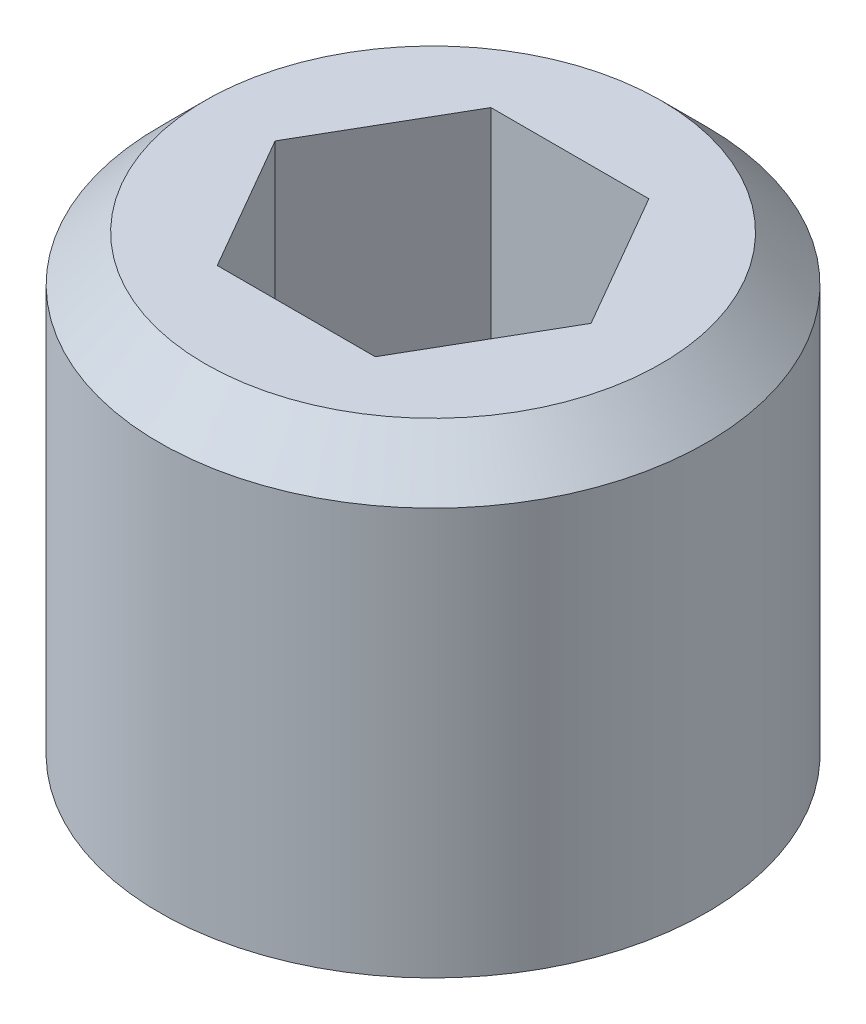
SolidWorks part; units mm, degrees
material "Alloy Steel"
ref_plane "Plane1" through (0, 0, 0) normal (0, 0, 1) x (1, 0, 0)
ref_plane "Plane2" through (0, 0, 0) normal (0, 1, 0) x (1, 0, 0)
ref_plane "Plane3" through (0, 0, 0) normal (1, 0, 0) x (0, 0, -1)
sketch "Sketch1" plane through (0, 0, 0) normal (0, 0, 1) x (1, 0, 0)
  line L0 (0, 0.3464) -> (0, 3)
  line L1 (0, 3) -> (1.25, 3)
  line L2 (0.6, 0) -> (0, 0.3464)
  line L3 (1.5, 2.75) -> (1.25, 3)
  line L4 (1.5, 2.75) -> (1.5, 0.5196)
  line L5 (1.5, 0.5196) -> (0.6, 0)
  line L6 (0, 3) -> (0, 5.6536) construction
  dimension "D6" = 3
  dimension "D1" = 0.25
  dimension "D2" = 0.25
  dimension "D3" = 3
  dimension "D4" = 1.2
  dimension "D5" = 60
  dimension "D7" = 30
revolve "Base-Revolve" add sketch "Sketch1" angle 360 about L6
cosmetic thread "Cosmetic Thread1" parameters "D2"=2.5
sketch "Sketch2" plane through (0, 3, 0) normal (0, 1, 0) x (-1, 0, 0)
  line L1 (-0.433, 0.75) -> (-0.866, 0)
  line L2 (-0.866, 0) -> (-0.433, -0.75)
  line L3 (-0.433, -0.75) -> (0.433, -0.75)
  line L4 (0.433, -0.75) -> (0.866, 0)
  line L5 (0.866, 0) -> (0.433, 0.75)
  line L6 (0.433, 0.75) -> (-0.433, 0.75)
  circle A0 centre (0, 0) radius 0.75 construction
  dimension "D1" = 1.5
extrude "Cut-Extrude1" cut sketch "Sketch2" against normal blind 2
